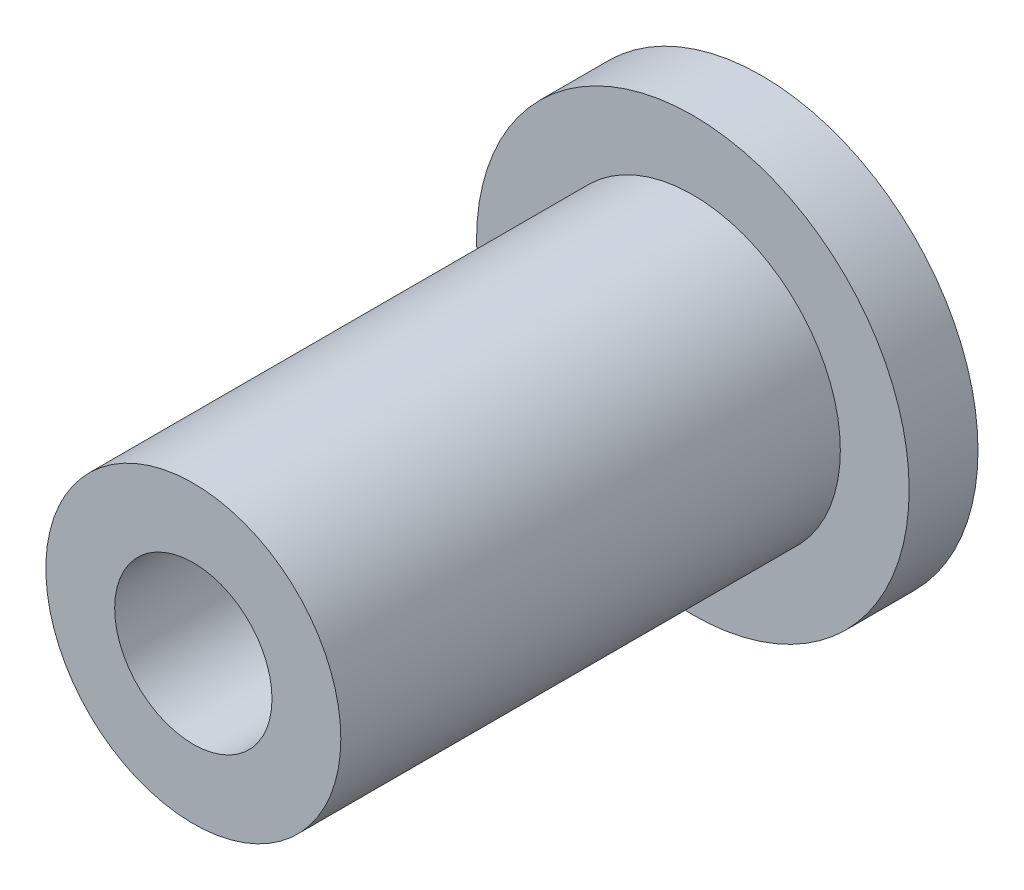
SolidWorks part; units mm, degrees
material "AISI 1020"
ref_plane "Front Plane" through (0, 0, 0) normal (0, 0, 1) x (1, 0, 0)
ref_plane "Top Plane" through (0, 0, 0) normal (0, 1, 0) x (1, 0, 0)
ref_plane "Right Plane" through (0, 0, 0) normal (1, 0, 0) x (0, 0, -1)
sketch "Sketch3" plane through (0, 0, 0) normal (0, 1, 0) x (1, 0, 0)
  circle A0 centre (0, 0) radius 10.287
  circle A1 centre (0, 0) radius 12.7
  dimension "D1" = 25.4
  dimension "D2" = 2.413
extrude "Boss-Extrude2" [suppressed] add sketch "Sketch3" along normal mid plane 250
sketch "Sketch5" plane through (0, 0, 0) normal (0, 0, 1) x (1, 0, 0)
  circle A0 centre (0, 0) radius 7.5
  dimension "D1" = 15
extrude "Cut-Extrude1" [suppressed] cut sketch "Sketch5" against normal through all both and the other way through all
sketch "Sketch1" plane through (0, 0, 0) normal (0, 0, 1) x (1, 0, 0)
  circle A0 centre (0, 0) radius 7.5
  circle A1 centre (0, 0) radius 4
  dimension "D1" = 8
  dimension "D2" = 15
extrude "Insert" add sketch "Sketch1" along normal mid plane 25.4
sketch "Sketch6" plane through (0, 0, 0) normal (0, 1, 0) x (1, 0, 0)
  line L0 (0, 17.1779) -> (0, -24.9983) construction
  line L2 (-11, 16.2) -> (-11, 12.7)
  line L3 (-11, 12.7) -> (-7.5, 12.7)
  line L4 (-7.5, 12.7) -> (-7.5, -12.7) construction
  line L5 (7.5, 12.7) -> (-7.5, 12.7) construction
  line L8 (-11, 16.2) -> (-7.5, 16.2)
  line L9 (-7.5, 16.2) -> (-4, 16.2)
  line L10 (-4, 16.2) -> (-4, 12.7)
  line L11 (-4, 12.7) -> (-7.5, 12.7)
  dimension "D2" = 3.5
  dimension "D3" = 4
revolve "Revolve5" add sketch "Sketch6" angle 360 about L0
equation "\"Critical Fastener Diameter\"= 8mm"
equation "\"D1@Sketch1\"= \"Critical Fastener Diameter\""
equation "\"Insert/Collar Thickness\"= 2.413mm"
equation "\"Tube with Holt Diameter\"= 25.4mm"
equation "\"D1@Insert\"= \"Tube with Holt Diameter\""
equation "\"Outer Diameter\"= 15mm"
equation "\"D2@Sketch1\"=\"Outer Diameter\""
equation "\"D1@Sketch3\"=1in"
equation "\"D2@Sketch3\"=0.095in"
equation "\"D1@Sketch5\"=\"Outer Diameter\""
equation "\"D2@Sketch6\"=(\"Outer Diameter\"-\"Critical Fastener Diameter\")/2"
equation "\"D3@Sketch6\"=\"Critical Fastener Diameter\"/2"
